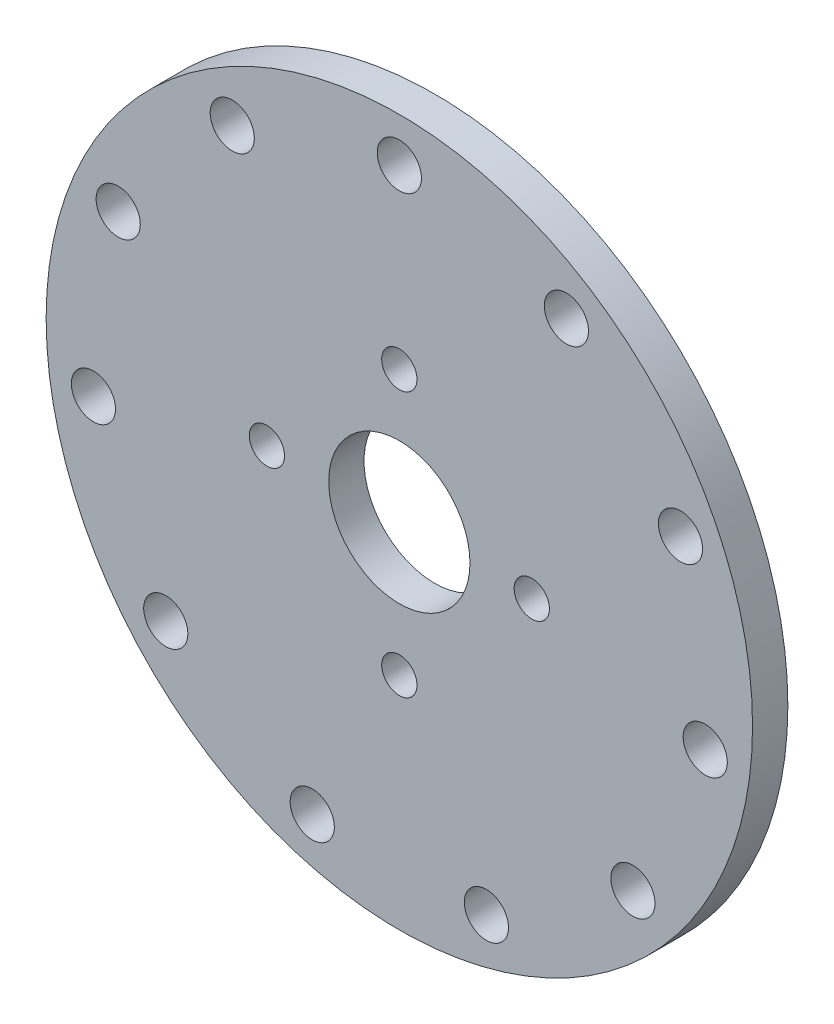
SolidWorks part; units mm, degrees
ref_plane "Front Plane" through (0, 0, 0) normal (0, 0, 1) x (1, 0, 0)
ref_plane "Top Plane" through (0, 0, 0) normal (0, 1, 0) x (1, 0, 0)
ref_plane "Right Plane" through (0, 0, 0) normal (1, 0, 0) x (0, 0, -1)
sketch "Sketch1" plane through (0, 0, 0) normal (0, 0, 1) x (1, 0, 0)
  circle A0 centre (0, 0) radius 40
  circle A1 centre (0, 0) radius 8
  dimension "D1" = 80
  dimension "D2" = 16
extrude "Boss-Extrude1" add sketch "Sketch1" along normal blind 4
sketch "Sketch2" plane through (0, 0, 4) normal (0, 0, 1) x (1, 0, 0)
  circle A0 centre (0, 0) radius 35 construction
  circle A1 centre (0, 35) radius 2.5
  circle A2 centre (18.9224, 29.4439) radius 2.5
  circle A3 centre (31.8371, 14.5395) radius 2.5
  circle A4 centre (34.6438, -4.981) radius 2.5
  circle A5 centre (26.4512, -22.9201) radius 2.5
  circle A6 centre (9.8606, -33.5823) radius 2.5
  circle A7 centre (-9.8606, -33.5823) radius 2.5
  circle A8 centre (-26.4512, -22.9201) radius 2.5
  circle A9 centre (-34.6438, -4.981) radius 2.5
  circle A10 centre (-31.8371, 14.5395) radius 2.5
  circle A11 centre (-18.9224, 29.4439) radius 2.5
  point P28 (0, 0)
  dimension "D1" = 70
  dimension "D2" = 5
  dimension "D3" = 11
extrude "Cut-Extrude1" cut sketch "Sketch2" against normal blind 4
sketch "Sketch3" plane through (0, 0, 4) normal (0, 0, 1) x (1, 0, 0)
  circle A0 centre (0, 0) radius 15 construction
  circle A1 centre (0, 15) radius 2
  circle A2 centre (15, 0) radius 2
  circle A3 centre (0, -15) radius 2
  circle A4 centre (-15, 0) radius 2
  point P14 (0, 0)
  dimension "D1" = 30
  dimension "D2" = 4
  dimension "D3" = 4
extrude "Cut-Extrude2" cut sketch "Sketch3" against normal blind 4
